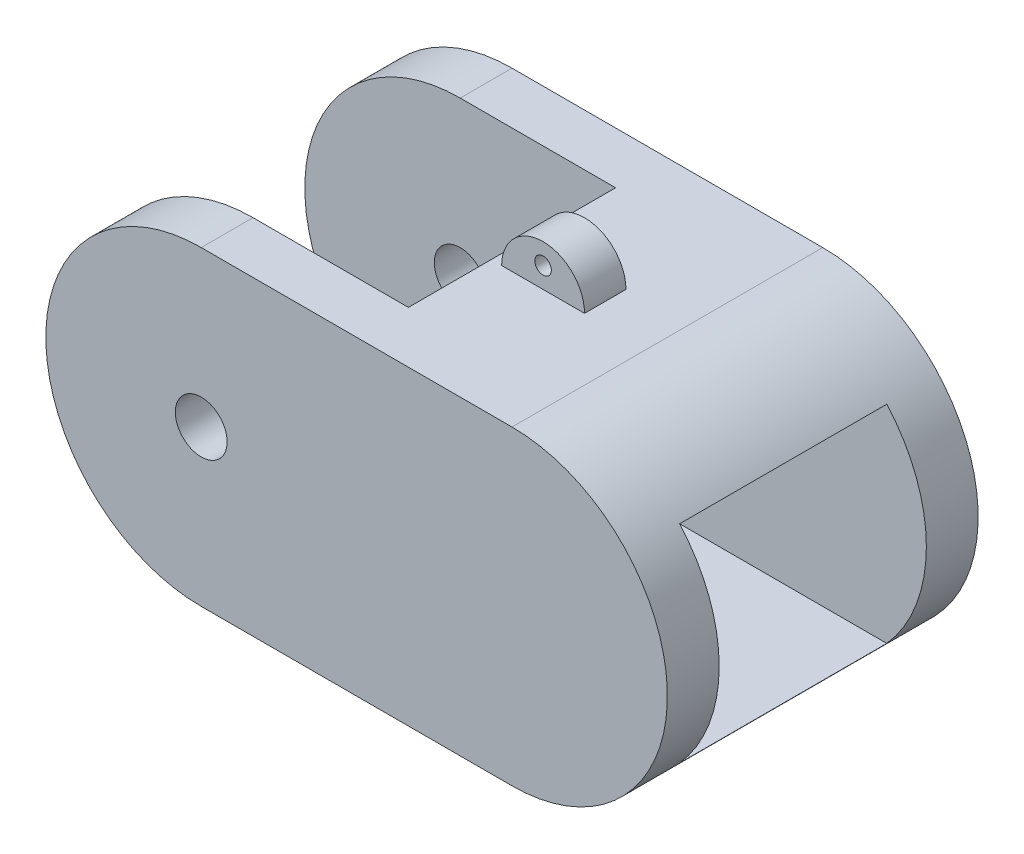
SolidWorks part; units mm, degrees
ref_plane "Front Plane" through (0, 0, 0) normal (0, 0, 1) x (1, 0, 0)
ref_plane "Top Plane" through (0, 0, 0) normal (0, 1, 0) x (1, 0, 0)
ref_plane "Right Plane" through (0, 0, 0) normal (1, 0, 0) x (0, 0, -1)
ref_plane "Right Side Plane" through (0, 0, 9.525) normal (0, 0, 1) x (1, 0, 0)
ref_plane "Inside Plane" through (0, 19.05, 0) normal (0, 1, 0) x (1, 0, 0)
ref_plane "Joint Plane" through (-15.875, 0, 0) normal (1, 0, 0) x (0, 0, -1)
sketch "Sketch1" plane through (0, 0, 0) normal (0, 1, 0) x (1, 0, 0)
  line L1 (-22.225, 9.525) -> (15.875, 9.525)
  line L2 (-22.225, 9.525) -> (-22.225, -9.525)
  line L3 (-22.225, -9.525) -> (15.875, -9.525)
  line L4 (15.875, 9.525) -> (15.875, -9.525)
  dimension "D1" = 38.1
  dimension "D2" = 19.05
  dimension "D3" = 9.525
  dimension "D4" = 15.875
extrude "Boss-Extrude1" add sketch "Sketch1" along normal blind 19.05
sketch "Sketch2" plane through (0, 0, 9.525) normal (0, 0, 1) x (1, 0, 0)
  line L0 (-22.225, 19.05) -> (15.875, 19.05) construction
  line L1 (-22.225, 19.05) -> (-22.225, 0) construction
  line L2 (-22.225, 0) -> (15.875, 0) construction
  line L3 (15.875, 19.05) -> (15.875, 0) construction
  circle A0 centre (-12.7, 9.525) radius 1.5875
  arc A1 (-12.7, 19.05) -> (-12.7, 0) centre (-12.7, 9.525) ccw
  arc A2 (-12.7, 19.05) -> (-12.7, 0) centre (-21.0188, 9.525) ccw
  arc A3 (6.35, 0) -> (6.35, 19.05) centre (6.35, 9.525) ccw
  arc A4 (6.35, 19.05) -> (6.35, 0) centre (13.21, 9.525) cw
extrude "Cut-Extrude2" cut sketch "Sketch2" against normal blind 19.05
sketch "Sketch3" plane through (0, 19.05, 0) normal (0, 1, 0) x (1, 0, 0)
  line L10 (-12.7, 9.525) -> (-12.7, -9.525) construction
  line L11 (-29.3201, 6.35) -> (-12.7, 6.35)
  line L12 (-29.3201, 6.35) -> (-29.3201, -6.35)
  line L13 (-29.3201, -6.35) -> (-12.7, -6.35)
  line L14 (-12.7, 6.35) -> (-12.7, -6.35)
  line L15 (-12.7, 9.525) -> (-22.225, 9.525) construction
  line L16 (-22.225, -9.525) -> (-12.7, -9.525) construction
  dimension "D1" = 3.175
  dimension "D2" = 3.175
extrude "Cut-Extrude3" cut sketch "Sketch3" against normal blind 19.05
sketch "Sketch4" plane through (-15.875, 0, 0) normal (1, 0, 0) x (0, 0, -1)
  line L0 (6.35, 11.1125) -> (6.35, 19.05) construction
  line L1 (6.35, 15.875) -> (-6.35, 15.875)
  line L2 (6.35, 15.875) -> (6.35, 3.175)
  line L3 (6.35, 3.175) -> (-6.35, 3.175)
  line L4 (-6.35, 15.875) -> (-6.35, 3.175)
  line L5 (-6.35, 0) -> (-6.35, 19.05) construction
  line L6 (7.6835, 19.05) -> (-7.6835, 19.05) construction
  line L7 (-6.35, 0) -> (6.35, 0) construction
  dimension "D1" = 3.175
  dimension "D2" = 3.175
extrude "Cut-Extrude4" cut sketch "Sketch4" along normal blind 50.8
sketch "Sketch6" plane through (0, 0, 0) normal (0, 1, 0) x (1, 0, 0)
  line L0 (-12.7, 6.35) -> (-12.7, -6.35) construction
  line L1 (-6.35, -1.905) -> (1.3106, -1.905)
  line L2 (-6.35, -1.905) -> (-6.35, 1.905)
  line L3 (-6.35, 1.905) -> (1.3106, 1.905)
  line L4 (1.3106, -1.905) -> (1.3106, 1.905)
  dimension "D1" = 3.81
  dimension "D3" = 6.35
  dimension "D4" = 1.905
extrude "Boss-Extrude2" add sketch "Sketch6" against normal blind 7.62
sketch "Sketch7" plane through (0, 0, 9.525) normal (0, 0, 1) x (1, 0, 0)
  line L0 (-7.0809, -3.1317) -> (-6.858, 0)
  line L3 (-6.604, 0) -> (-6.604, -7.62) construction
  line L8 (-6.858, 0) -> (-6.858, -7.7678)
  line L9 (-6.858, -7.7678) -> (-14.771, -7.7678)
  line L10 (-14.771, -7.7678) -> (-14.771, 0)
  line L11 (-14.771, 0) -> (-9.975, 0)
  line L12 (1.563, 0) -> (-3.233, 0)
  line L13 (1.563, -7.7678) -> (1.563, 0)
  line L14 (-6.35, -7.7678) -> (1.563, -7.7678)
  line L15 (-6.35, 0) -> (-6.35, -7.7678)
  line L16 (-6.1271, -3.1317) -> (-6.35, 0)
  line L17 (-6.35, -7.62) -> (-6.35, 0) construction
  arc A9 (-8.7944, -2.6143) -> (-9.975, 0) centre (-13.1218, -2.9949) ccw
  arc A10 (-10.1635, -4.3117) -> (-8.7944, -2.6143) centre (-10.9395, -2.285) ccw
  arc A11 (-11.8934, -2.9278) -> (-10.1635, -4.3117) centre (-9.8847, -2.19) ccw
  arc A12 (-10.9962, -2.3329) -> (-11.8934, -2.9278) centre (-11.2469, -2.9288) ccw
  arc A13 (-11.3011, -1.1267) -> (-10.9962, -2.3329) centre (-11.1487, -1.7298) cw
  arc A14 (-13.0445, -2.7718) -> (-11.3011, -1.1267) centre (-11.3965, -2.7719) cw
  arc A15 (-9.5958, -5.7694) -> (-7.0809, -3.1317) centre (-10.0544, -2.8145) ccw
  arc A16 (-13.0445, -2.7718) -> (-9.5958, -5.7694) centre (-10.0544, -2.8145) ccw
  arc A17 (-0.1635, -2.7718) -> (-3.6122, -5.7694) centre (-3.1536, -2.8145) cw
  arc A18 (-3.6122, -5.7694) -> (-6.1271, -3.1317) centre (-3.1536, -2.8145) cw
  arc A19 (-0.1635, -2.7718) -> (-1.9069, -1.1267) centre (-1.8115, -2.7719) ccw
  arc A20 (-1.9069, -1.1267) -> (-2.2118, -2.3329) centre (-2.0593, -1.7298) ccw
  arc A21 (-2.2118, -2.3329) -> (-1.3146, -2.9278) centre (-1.9611, -2.9288) cw
  arc A22 (-1.3146, -2.9278) -> (-3.0445, -4.3117) centre (-3.3233, -2.19) cw
  arc A23 (-3.0445, -4.3117) -> (-4.4136, -2.6143) centre (-2.2685, -2.285) cw
  arc A24 (-4.4136, -2.6143) -> (-3.233, 0) centre (-0.0862, -2.9949) cw
  point P46 (1.563, -7.7678)
  dimension "D1" = 0.254
  dimension "D2" = 0.254
extrude "Cut-Extrude6" cut sketch "Sketch7" against normal blind 19.05
sketch "Sketch8" plane through (0, 19.05, 0) normal (0, 1, 0) x (1, 0, 0)
  line L1 (-2.54, 1.27) -> (2.54, 1.27)
  line L2 (-2.54, 1.27) -> (-2.54, -1.27)
  line L3 (-2.54, -1.27) -> (2.54, -1.27)
  line L4 (2.54, 1.27) -> (2.54, -1.27)
  dimension "D1" = 2.54
  dimension "D2" = 5.08
  dimension "D3" = 2.54
  dimension "D4" = 1.27
extrude "Boss-Extrude3" add sketch "Sketch8" along normal blind 2.54
sketch "Sketch9" plane through (0, 0, 9.525) normal (0, 0, 1) x (1, 0, 0)
  line L0 (-2.54, 19.05) -> (2.54, 19.05) construction
  line L1 (2.54, 21.59) -> (2.54, 19.05) construction
  line L2 (-2.54, 21.59) -> (2.54, 21.59) construction
  arc A0 (-2.54, 19.05) -> (2.54, 19.05) centre (0, 19.05) cw
  circle A1 centre (0, 20.32) radius 0.508
  arc A2 (-2.54, 19.05) -> (2.54, 19.05) centre (0, 20.4722) cw
  dimension "D1" = 1.27
  dimension "D2" = 2.54
extrude "Cut-Extrude7" cut sketch "Sketch9" against normal blind 19.05
sketch "Sketch10" plane through (0, 19.05, 0) normal (0, 1, 0) x (1, 0, 0)
  line L1 (-12.7, 6.35) -> (-3.175, 6.35)
  line L2 (-12.7, 6.35) -> (-12.7, -6.35)
  line L3 (-12.7, -6.35) -> (-3.175, -6.35)
  line L4 (-3.175, 6.35) -> (-3.175, -6.35)
  dimension "D1" = 9.525
extrude "Cut-Extrude8" cut sketch "Sketch10" against normal blind 3.81
